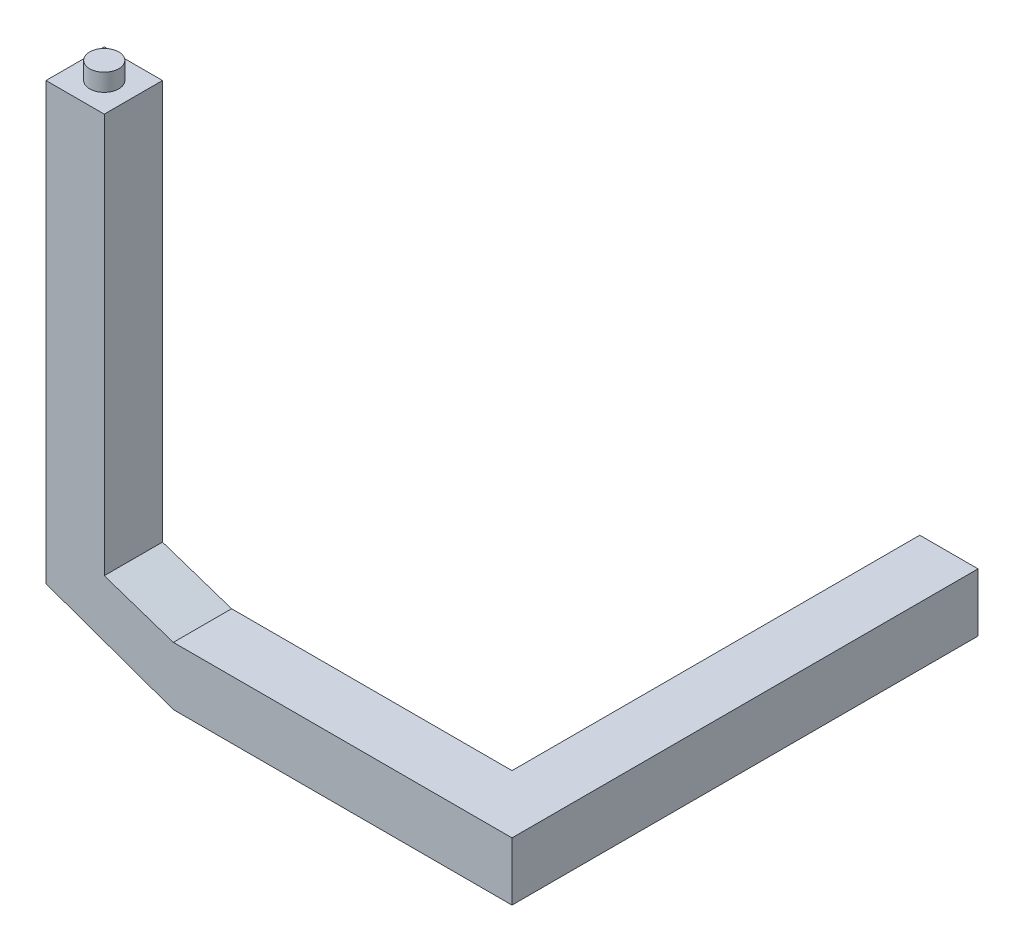
SolidWorks part; units mm, degrees
ref_plane "Front Plane" through (0, 0, 0) normal (0, 0, 1) x (1, 0, 0)
ref_plane "Top Plane" through (0, 0, 0) normal (0, 1, 0) x (1, 0, 0)
ref_plane "Right Plane" through (0, 0, 0) normal (1, 0, 0) x (0, 0, -1)
sketch "Sketch1" plane through (0, 0, 0) normal (0, 0, 1) x (1, 0, 0)
  line L0 (0, 0) -> (100, 0)
  line L1 (100, 0) -> (100, 100)
  line L2 (100, 100) -> (0, 100)
  line L3 (0, 100) -> (0, 0)
  dimension "D1" = 100
  dimension "D2" = 100
extrude "Boss-Extrude1" add sketch "Sketch1" along normal blind 800
sketch "Sketch2" plane through (0, 0, 0) normal (1, 0, 0) x (0, 0, -1)
  line L0 (-800, 100) -> (-700, 100)
  line L1 (-800, 100) -> (0, 100) construction
  line L2 (-700, 100) -> (-700, 0)
  line L3 (-800, 0) -> (0, 0) construction
  line L4 (-700, 0) -> (-800, 0)
  line L5 (-800, 0) -> (-800, 100)
  dimension "D1" = 100
extrude "Boss-Extrude2" add sketch "Sketch2" against normal blind 700
sketch "Sketch3" plane through (0, 0, 0) normal (0, 0, 1) x (1, 0, 0)
  line L0 (-481.3742, 100) -> (-700, 15.6312)
  line L1 (-700, 0) -> (-700, 100) construction
  line L2 (-1713.3699, -375.4331) -> (-481.3742, 100) construction
  line L3 (-700, 15.6312) -> (-700, 100)
  line L4 (-700, 100) -> (-481.3742, 100)
ref_plane "Plane1" through (0, 0, 800) normal (0, 0, 1) x (1, 0, 0)
sketch "Sketch4" plane through (0, 0, 800) normal (0, 0, 1) x (1, 0, 0)
  line L0 (-493.991, 0) -> (-600, -41.5645)
  line L1 (-700, 0) -> (100, 0) construction
  line L2 (-493.9453, 0.0179) -> (-1705.8453, -475.1496) construction
  line L7 (-700, 0) -> (-493.991, 0)
  line L8 (-700, -730.3561) -> (-600, -730.3561)
  line L9 (-600, -730.3561) -> (-600, -41.5645)
  line L10 (-700, 0) -> (-700, -730.3561)
extrude "Boss-Extrude3" add sketch "Sketch4" against normal blind 100 contours L7 L0 L9 L8 L10
ref_plane "Plane2" through (0, -730.3561, 0) normal (0, -1, 0) x (-1, 0, 0)
sketch "Sketch5" plane through (0, -730.3561, 0) normal (0, -1, 0) x (-1, 0, 0)
  line L0 (650, -700) -> (650, -800)
  line L1 (700, -700) -> (600, -700) construction
  line L2 (700, -800) -> (600, -800) construction
  circle A0 centre (650, -750) radius 25
extrude "Boss-Extrude4" add sketch "Sketch5" along normal blind 25 contours A0
sketch "Sketch6" plane through (0, 0, 800) normal (0, 0, 1) x (1, 0, 0)
  line L3 (-700, 100) -> (-700, -730.3561) construction
  line L8 (-700, 0) -> (-700, 77.8729)
  line L15 (-493.991, 0) -> (100, 0) construction
  line L16 (-481.3742, 0) -> (-700, 0)
  line L17 (-700, 77.8729) -> (-481.3742, 0)
extrude "Cut-Extrude2" cut sketch "Sketch6" against normal through all contours L17 L16 L8
sketch "Sketch8" plane through (0, 0, 800) normal (0, 0, 1) x (1, 0, 0)
  line L0 (-600, -41.5645) -> (-600, 0)
  line L1 (-493.991, 0) -> (-700, 0) construction
  line L2 (-700, 100) -> (-600, 100)
  line L3 (-700, 100) -> (-481.3742, 100) construction
  line L4 (-600, 139.7642) -> (-600, 826.0357)
  line L5 (-600, 139.7642) -> (-481.3742, 100)
  line L6 (-600, 826.0357) -> (-700, 826.0357)
  line L7 (-700, 826.0357) -> (-700, 100)
  line L8 (-600, 100) -> (-481.3742, 100)
extrude "Boss-Extrude5" add sketch "Sketch8" against normal blind 100 contours L4 L6 L7 L2 L8 L5
sketch "Sketch9" plane through (0, 0, 800) normal (0, 0, 1) x (1, 0, 0)
  line L0 (-740.3533, 0) -> (-493.3646, 0)
  line L1 (-493.3646, 0) -> (-493.3646, -882.4817)
  line L2 (-493.3646, -882.4817) -> (-837.9906, -863.8824)
  line L3 (-837.9906, -863.8824) -> (-740.3533, 0)
extrude "Cut-Extrude3" cut sketch "Sketch9" against normal through all
ref_plane "Plane4" through (0, 826.0357, 0) normal (0, 1, 0) x (1, 0, 0)
sketch "Sketch10" plane through (0, 826.0357, 0) normal (0, 1, 0) x (1, 0, 0)
  line L0 (-650, -700) -> (-650, -800)
  line L1 (-600, -700) -> (-700, -700) construction
  line L2 (-440, -800) -> (440, -800) construction
  circle A0 centre (-650, -750) radius 25
extrude "Boss-Extrude6" add sketch "Sketch10" along normal blind 30 contours A0
